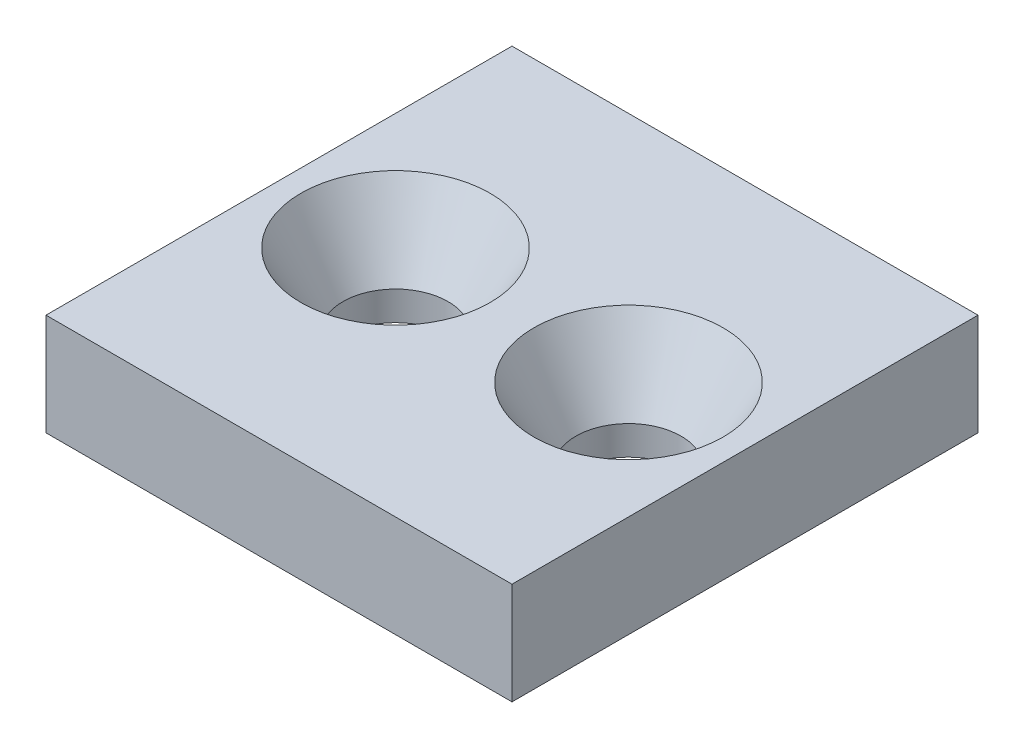
SolidWorks part; units mm, degrees
ref_plane "Front Plane" through (0, 0, 0) normal (0, 0, 1) x (1, 0, 0)
ref_plane "Top Plane" through (0, 0, 0) normal (0, 1, 0) x (1, 0, 0)
ref_plane "Right Plane" through (0, 0, 0) normal (1, 0, 0) x (0, 0, -1)
sketch "Sketch1" plane through (0, 0, 0) normal (0, 1, 0) x (1, 0, 0)
  line L1 (-16, -16) -> (16, -16)
  line L2 (-16, -16) -> (-16, 16)
  line L3 (-16, 16) -> (16, 16)
  line L4 (16, -16) -> (16, 16)
  line L5 (0, 16) -> (0, -16) construction
  line L6 (-16, 0) -> (16, 0) construction
  point P0 (0, 0)
  dimension "D1" = 32
  dimension "D2" = 32
extrude "Boss-Extrude1" add sketch "Sketch1" along normal mid plane 7
sketch "Sketch2" plane through (0, 0, 0) normal (0, 0, 1) x (1, 0, 0)
  line L0 (8, 3.5) -> (14.5, 3.5)
  line L1 (11.6132, -1.5) -> (11.6132, -3.5)
  line L2 (11.6132, -3.5) -> (8, -3.5)
  line L3 (0, 0) -> (0, -0.9713) construction
  line L4 (8, 3.5) -> (8, -3.5)
  line L5 (-16, -3.5) -> (16, -3.5) construction
  line L6 (-16, 3.5) -> (16, 3.5) construction
  line L7 (14.5, 3.5) -> (11.6132, -1.5)
  line L8 (-11.6132, -3.5) -> (-8, -3.5) construction
  line L9 (-11.6132, -1.5) -> (-11.6132, -3.5) construction
  line L10 (-8, 3.5) -> (-14.5, 3.5) construction
  line L11 (-14.5, 3.5) -> (-11.6132, -1.5) construction
  line L12 (-8, 3.5) -> (-8, -3.5) construction
  dimension "D1" = 5
  dimension "D3" = 6.5
  dimension "D4" = 7
revolve "Cut-Revolve1" cut sketch "Sketch2" angle 360 about L4
mirror "Mirror1" about plane through (0, 0, 0) normal (1, 0, 0) of "Cut-Revolve1"
